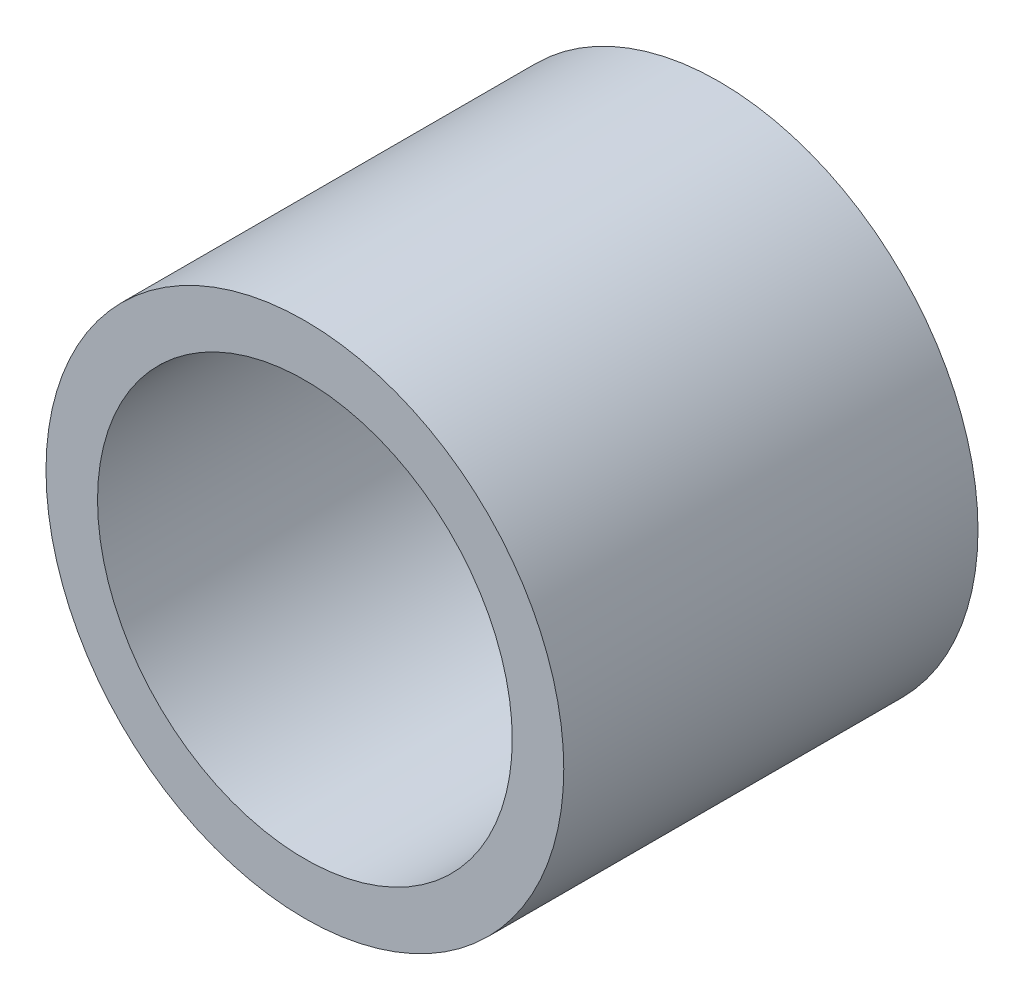
SolidWorks part; units mm, degrees
ref_plane "Front Plane" through (0, 0, 0) normal (0, 0, 1) x (1, 0, 0)
ref_plane "Top Plane" through (0, 0, 0) normal (0, 1, 0) x (1, 0, 0)
ref_plane "Right Plane" through (0, 0, 0) normal (1, 0, 0) x (0, 0, -1)
sketch "Sketch1" plane through (0, 0, 0) normal (0, 0, 1) x (1, 0, 0)
  circle A0 centre (0, 0) radius 3.9688
  circle A1 centre (0, 0) radius 3.1788
  point P4 (0, 3.9688)
  dimension "OD" = 7.9375
  dimension "ID" = 6.3576
sketch "Sketch2" plane through (0, 0, 0) normal (1, 0, 0) x (0, 0, -1)
  line L0 (3.175, 0) -> (-3.175, 0) construction
  line L1 (3.175, 3.9688) -> (-3.175, 3.9687) construction
  point P4 (0, 0)
  point P9 (0, 3.9688)
  dimension "Length" = 6.35
sketch "Sketch3" plane through (0, 0, 0) normal (0, 0, 1) x (1, 0, 0)
  circle A0 centre (0, 0) radius 3.9688 construction
  circle A1 centre (0, 0) radius 3.1788 construction
  circle A2 centre (0, 0) radius 3.9688
  circle A3 centre (0, 0) radius 3.1788
extrude "Boss-Extrude1" add sketch "Sketch3" against normal up to vertex (3.175 mm away) and the other way up to vertex (3.175 mm away) up to point (0, 0, -3.175) other way up to point (0, 0, 3.175)
